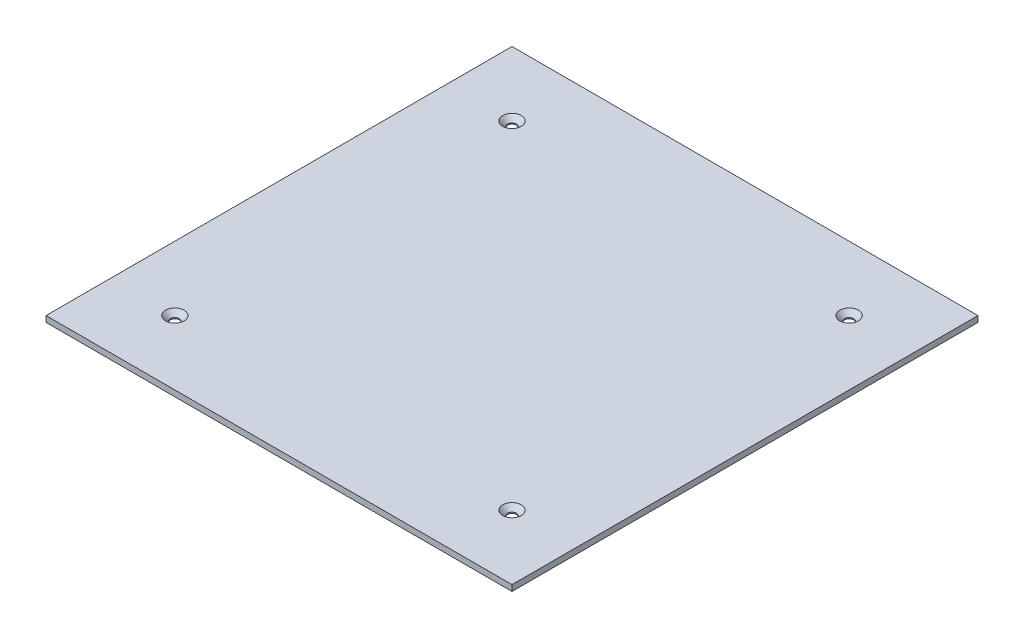
SolidWorks part; units mm, degrees
ref_plane "Front Plane" through (0, 0, 0) normal (0, 0, 1) x (1, 0, 0)
ref_plane "Top Plane" through (0, 0, 0) normal (0, 1, 0) x (1, 0, 0)
ref_plane "Right Plane" through (0, 0, 0) normal (1, 0, 0) x (0, 0, -1)
sketch "Sketch1" plane through (0, 0, 0) normal (0, 1, 0) x (1, 0, 0)
  line L1 (117.5, 117.5) -> (-117.5, 117.5)
  line L2 (117.5, 117.5) -> (117.5, -117.5)
  line L3 (117.5, -117.5) -> (-117.5, -117.5)
  line L4 (-117.5, 117.5) -> (-117.5, -117.5)
  line L5 (0, -117.5) -> (0, 117.5) construction
  line L6 (117.5, 0) -> (-117.5, 0) construction
  point P0 (0, 0)
  dimension "D1" = 235
  dimension "D2" = 235
extrude "Boss-Extrude1" add sketch "Sketch1" along normal blind 3 contours L2 L3 L4 L1
hole_wizard "CSK for M4 Flat Head Machine Screw1" positions "Sketch4" profile "Sketch3" countersink size "M4" standard "ANSI Metric" end condition through all
sketch "Sketch4" plane through (0, 3, 0) normal (0, 1, 0) x (1, 0, 0)
  line L0 (-85, 85) -> (85, 85) construction
  line L1 (-85, 85) -> (-85, -85) construction
  line L4 (-85, -85) -> (85, 85) construction
  point P0 (-85, 85)
  point P7 (85, 85)
  point P8 (85, -85)
  point P9 (-85, -85)
  dimension "D4" = 170
  dimension "D5" = 170
  dimension "D1" = 2
  dimension "D2" = 2
sketch "Sketch3" plane through (-85, 3, -85) normal (1, 0, 0) x (0, 0, 1)
  line L0 (0, 0) -> (0, 3)
  line L1 (0, 3) -> (2.25, 3)
  line L2 (2.25, 3) -> (2.25, 2.45)
  line L3 (2.25, 2.45) -> (4.7, 0)
  line L5 (4.7, 0) -> (0, 0)
  line L6 (-2.25, 2.45) -> (-4.7, 0) construction
  line L11 (0, -6.35) -> (0, 107.95) construction
  dimension "Thru Hole Dia." = 4.5
  dimension "Thru Hole Depth" = 3
  dimension "Near C'Sink Dia." = 9.4
  dimension "Near C'Sink Angle" = 90
sketch "Sketch6" [suppressed] plane through (0, 1.6, 0) normal (0, 1, 0) x (1, 0, 0)
  line L1 (128, 128) -> (-128, 128)
  line L2 (128, 128) -> (128, -128)
  line L3 (128, -128) -> (-128, -128)
  line L4 (-128, 128) -> (-128, -128)
  line L5 (0, -128) -> (0, 128) construction
  line L6 (128, 0) -> (-128, 0) construction
  line L10 (-117.5, 117.5) -> (-117.5, -117.5)
  line L11 (-117.5, -117.5) -> (117.5, -117.5)
  line L12 (117.5, -117.5) -> (117.5, 117.5)
  line L13 (117.5, 117.5) -> (-117.5, 117.5)
  line L14 (-117.5, 117.5) -> (-117.5, -117.5)
  line L15 (-117.5, -117.5) -> (117.5, -117.5)
  line L16 (117.5, -117.5) -> (117.5, 117.5)
  line L17 (117.5, 117.5) -> (-117.5, 117.5)
  point P0 (0, 0)
  dimension "D1" = 256
  dimension "D2" = 256
  dimension "D3" = 0
extrude "Boss-Extrude3" [suppressed] add sketch "Sketch6" against normal blind 1 separate body
sketch "Sketch7" [suppressed] plane through (0, 1.6, 0) normal (0, 1, 0) x (1, 0, 0)
  line L1 (-155, -155) -> (155, -155)
  line L2 (-155, -155) -> (-155, 155)
  line L3 (-155, 155) -> (155, 155)
  line L4 (155, -155) -> (155, 155)
  line L5 (0, 155) -> (0, -155) construction
  line L6 (-155, 0) -> (155, 0) construction
  line L10 (-128, 128) -> (-128, -128)
  line L11 (-128, -128) -> (128, -128)
  line L12 (128, -128) -> (128, 128)
  line L13 (128, 128) -> (-128, 128)
  line L14 (-128, 128) -> (-128, -128)
  line L15 (-128, -128) -> (128, -128)
  line L16 (128, -128) -> (128, 128)
  line L17 (128, 128) -> (-128, 128)
  point P0 (0, 0)
  dimension "D1" = 310
  dimension "D2" = 310
  dimension "D3" = 0
extrude "Boss-Extrude4" [suppressed] add sketch "Sketch7" against normal blind 1 separate body
sketch "Sketch8" plane through (0, 3, 0) normal (0, 1, 0) x (1, 0, 0)
  line L1 (110, 110) -> (-110, 110)
  line L2 (110, 110) -> (110, -110)
  line L3 (110, -110) -> (-110, -110)
  line L4 (-110, 110) -> (-110, -110)
  line L5 (0, -110) -> (0, 110) construction
  line L6 (110, 0) -> (-110, 0) construction
  point P0 (0, 0)
  dimension "D1" = 220
sketch "Sketch9" plane through (0, 0, 0) normal (0, -1, 0) x (1, 0, 0)
  line L0 (117.5, -117.5) -> (-117.5, -117.5) construction
  line L1 (-69.5, -109.5) -> (-59.5, -109.5)
  line L2 (-69.5, -109.5) -> (-69.5, -97.5)
  line L3 (-69.5, -97.5) -> (-59.5, -97.5)
  line L4 (-59.5, -109.5) -> (-59.5, -97.5)
  line L5 (-64.5, -97.5) -> (-64.5, -109.5) construction
  line L6 (-69.5, -103.5) -> (-59.5, -103.5) construction
  line L7 (-52.5, -115.5) -> (-35.5, -115.5)
  line L8 (-52.5, -115.5) -> (-52.5, -95.5)
  line L9 (-52.5, -95.5) -> (-35.5, -95.5)
  line L10 (-35.5, -115.5) -> (-35.5, -95.5)
  line L11 (-44, -95.5) -> (-44, -115.5) construction
  line L12 (-52.5, -105.5) -> (-35.5, -105.5) construction
  line L14 (-117.5, -117.5) -> (-117.5, 117.5) construction
  point P216 (-64.5, -103.5)
  point P285 (-44, -105.5)
  dimension "D7" = 48
  dimension "D1" = 10
  dimension "D2" = 12
  dimension "D3" = 17
  dimension "D4" = 2
  dimension "D5" = 65
  dimension "D6" = 8
  dimension "D8" = 20
extrude "Boss-Extrude5" add sketch "Sketch9" along normal blind 15
